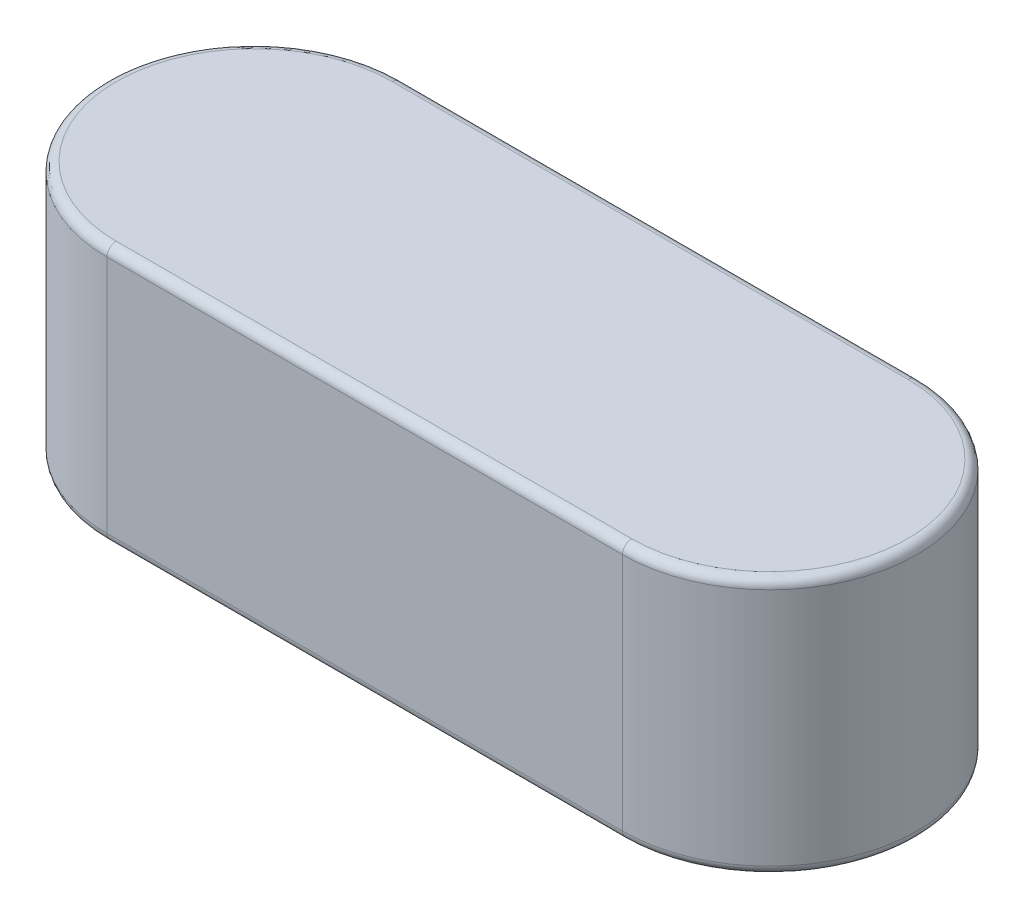
SolidWorks part; units mm, degrees
ref_plane "Front Plane" through (0, 0, 0) normal (0, 0, 1) x (1, 0, 0)
ref_plane "Top Plane" through (0, 0, 0) normal (0, 1, 0) x (1, 0, 0)
ref_plane "Right Plane" through (0, 0, 0) normal (1, 0, 0) x (0, 0, -1)
sketch "Sketch1" plane through (0, 0, 0) normal (0, 1, 0) x (1, 0, 0)
  line L1 (-14, 4) -> (0, 4)
  line L3 (-14, -4) -> (0, -4)
  arc A0 (0, -4) -> (0, 4) centre (0, 0) ccw
  arc A1 (-14, 4) -> (-14, -4) centre (-14, 0) ccw
  dimension "l" = 22
  dimension "b" = 8
extrude "Extrude1" add sketch "Sketch1" along normal blind 7
fillet "Fillet1" radius 0.25 8 edges at (-7, 0, -4) (4, 0, 0) (-18, 0, 0) (-7, 0, 4) (4, 7, 0) (-7, 7, 4) (-7, 7, -4) (-18, 7, 0)
